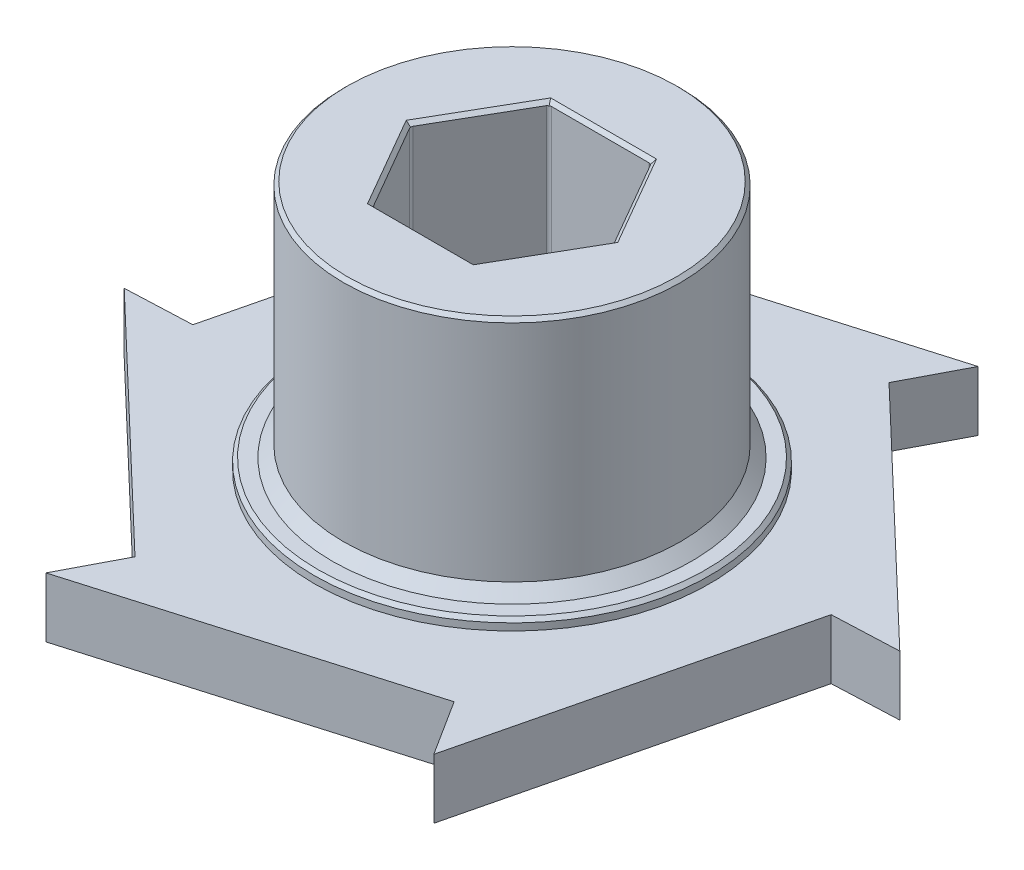
SolidWorks part; units mm, degrees
ref_plane "Front Plane" through (0, 0, 0) normal (0, 0, 1) x (1, 0, 0)
ref_plane "Top Plane" through (0, 0, 0) normal (0, 1, 0) x (1, 0, 0)
ref_plane "Right Plane" through (0, 0, 0) normal (1, 0, 0) x (0, 0, -1)
sketch "Sketch1" plane through (0, 0, 0) normal (0, 0, 1) x (1, 0, 0)
  line L0 (27.7876, 7.366) -> (0, 7.366)
  line L1 (0, 7.366) -> (0, 3.048)
  line L2 (0, 3.048) -> (27.7876, 3.048)
  line L3 (27.7876, 3.048) -> (27.7876, 7.366)
  line L4 (0, 7.366) -> (0, 3.048) construction
revolve "Revolve1" add sketch "Sketch1" angle 360 about L4
sketch "Sketch2" plane through (0, 7.366, 0) normal (0, 1, 0) x (-1, 0, 0)
  line L0 (27.7422, 1.5875) -> (25.86, 1.5875)
  line L1 (25.86, -1.5875) -> (27.7422, -1.5875)
  arc A0 (25.86, 1.5875) -> (25.86, -1.5875) centre (23.8125, 0) cw
  arc A1 (27.7422, -1.5875) -> (27.7422, 1.5875) centre (0, 0) ccw
extrude "Cut-Extrude1" cut sketch "Sketch2" against normal through all
sketch "Sketch3" plane through (0, 7.366, 0) normal (0, 1, 0) x (-1, 0, 0)
  arc A0 (27.522, -3.8329) -> (24.9505, -5.2112) centre (23.8125, 0) cw
  arc A1 (24.9505, -5.2112) -> (16.9883, -19.0022) centre (0, 0) cw
  arc A2 (16.9883, -19.0022) -> (17.0804, -21.9183) centre (11.9062, -20.6222) cw
  arc A3 (17.0804, -21.9183) -> (27.522, -3.8329) centre (0, 0) ccw
extrude "Cut-Extrude2" cut sketch "Sketch3" against normal through all
sketch "Sketch4" plane through (0, 7.366, 0) normal (0, 1, 0) x (-1, 0, 0)
  line L0 (15.2459, -23.2317) -> (14.3048, -21.6016)
  line L1 (11.5552, -23.1891) -> (12.4963, -24.8192)
  arc A0 (14.3048, -21.6016) -> (11.5552, -23.1891) centre (11.9063, -20.6222) cw
  arc A1 (12.4963, -24.8192) -> (15.2459, -23.2317) centre (0, 0) ccw
extrude "Cut-Extrude3" cut sketch "Sketch4" against normal through all
sketch "Sketch5" plane through (0, 7.366, 0) normal (0, 1, 0) x (-1, 0, 0)
  arc A0 (10.4416, -25.7512) -> (7.9622, -24.2134) centre (11.9063, -20.6222) cw
  arc A1 (7.9622, -24.2134) -> (-7.9622, -24.2134) centre (0, 0) cw
  arc A2 (-7.9622, -24.2134) -> (-10.4416, -25.7512) centre (-11.9063, -20.6222) cw
  arc A3 (-10.4416, -25.7512) -> (10.4416, -25.7512) centre (0, 0) ccw
extrude "Cut-Extrude4" cut sketch "Sketch5" against normal through all
sketch "Sketch6" plane through (0, 7.366, 0) normal (0, 1, 0) x (-1, 0, 0)
  line L0 (-12.4963, -24.8192) -> (-11.5552, -23.1891)
  line L1 (-14.3048, -21.6016) -> (-15.2459, -23.2317)
  arc A0 (-11.5552, -23.1891) -> (-14.3048, -21.6016) centre (-11.9062, -20.6222) cw
  arc A1 (-15.2459, -23.2317) -> (-12.4963, -24.8192) centre (0, 0) ccw
extrude "Cut-Extrude5" cut sketch "Sketch6" against normal through all
sketch "Sketch7" plane through (0, 7.366, 0) normal (0, 1, 0) x (-1, 0, 0)
  arc A0 (-17.0804, -21.9183) -> (-16.9883, -19.0022) centre (-11.9062, -20.6222) cw
  arc A1 (-16.9883, -19.0022) -> (-24.9505, -5.2112) centre (0, 0) cw
  arc A2 (-24.9505, -5.2112) -> (-27.522, -3.8329) centre (-23.8125, 0) cw
  arc A3 (-27.522, -3.8329) -> (-17.0804, -21.9183) centre (0, 0) ccw
extrude "Cut-Extrude6" cut sketch "Sketch7" against normal through all
sketch "Sketch8" plane through (0, 7.366, 0) normal (0, 1, 0) x (-1, 0, 0)
  line L0 (-27.7422, -1.5875) -> (-25.86, -1.5875)
  line L1 (-25.86, 1.5875) -> (-27.7422, 1.5875)
  arc A0 (-25.86, -1.5875) -> (-25.86, 1.5875) centre (-23.8125, 0) cw
  arc A1 (-27.7422, 1.5875) -> (-27.7422, -1.5875) centre (0, 0) ccw
extrude "Cut-Extrude7" cut sketch "Sketch8" against normal through all
sketch "Sketch9" plane through (0, 7.366, 0) normal (0, 1, 0) x (-1, 0, 0)
  arc A0 (-27.522, 3.8329) -> (-24.9505, 5.2112) centre (-23.8125, 0) cw
  arc A1 (-24.9505, 5.2112) -> (-16.9883, 19.0022) centre (0, 0) cw
  arc A2 (-16.9883, 19.0022) -> (-17.0804, 21.9183) centre (-11.9062, 20.6222) cw
  arc A3 (-17.0804, 21.9183) -> (-27.522, 3.8329) centre (0, 0) ccw
extrude "Cut-Extrude8" cut sketch "Sketch9" against normal through all
sketch "Sketch10" plane through (0, 7.366, 0) normal (0, 1, 0) x (-1, 0, 0)
  line L0 (-15.2459, 23.2317) -> (-14.3048, 21.6016)
  line L1 (-11.5552, 23.1891) -> (-12.4963, 24.8192)
  arc A0 (-14.3048, 21.6016) -> (-11.5552, 23.1891) centre (-11.9063, 20.6222) cw
  arc A1 (-12.4963, 24.8192) -> (-15.2459, 23.2317) centre (0, 0) ccw
extrude "Cut-Extrude9" cut sketch "Sketch10" against normal through all
sketch "Sketch11" plane through (0, 7.366, 0) normal (0, 1, 0) x (-1, 0, 0)
  arc A0 (-10.4416, 25.7512) -> (-7.9622, 24.2134) centre (-11.9062, 20.6222) cw
  arc A1 (-7.9622, 24.2134) -> (7.9622, 24.2134) centre (0, 0) cw
  arc A2 (7.9622, 24.2134) -> (10.4416, 25.7512) centre (11.9063, 20.6222) cw
  arc A3 (10.4416, 25.7512) -> (-10.4416, 25.7512) centre (0, 0) ccw
extrude "Cut-Extrude10" cut sketch "Sketch11" against normal through all
sketch "Sketch12" plane through (0, 7.366, 0) normal (0, 1, 0) x (-1, 0, 0)
  line L0 (12.4963, 24.8192) -> (11.5552, 23.1891)
  line L1 (14.3048, 21.6016) -> (15.2459, 23.2317)
  arc A0 (11.5552, 23.1891) -> (14.3048, 21.6016) centre (11.9062, 20.6222) cw
  arc A1 (15.2459, 23.2317) -> (12.4963, 24.8192) centre (0, 0) ccw
extrude "Cut-Extrude11" cut sketch "Sketch12" against normal through all
sketch "Sketch13" plane through (0, 7.366, 0) normal (0, 1, 0) x (-1, 0, 0)
  arc A0 (17.0804, 21.9183) -> (16.9883, 19.0022) centre (11.9062, 20.6222) cw
  arc A1 (16.9883, 19.0022) -> (24.9505, 5.2112) centre (0, 0) cw
  arc A2 (24.9505, 5.2112) -> (27.522, 3.8329) centre (23.8125, 0) cw
  arc A3 (27.522, 3.8329) -> (17.0804, 21.9183) centre (0, 0) ccw
extrude "Cut-Extrude12" cut sketch "Sketch13" against normal through all
sketch "Sketch14" plane through (0, 3.048, 0) normal (0, -1, 0) x (1, 0, 0)
  circle A0 centre (0, 0) radius 14.2748
extrude "Boss-Extrude1" add sketch "Sketch14" along normal blind 1.524
sketch "Sketch15" plane through (0, 1.524, 0) normal (0, -1, 0) x (1, 0, 0)
  circle A0 centre (0, 0) radius 9.2382
extrude "Boss-Extrude2" add sketch "Sketch15" along normal blind 1.524
sketch "Sketch16" plane through (0, 7.366, 0) normal (0, 1, 0) x (-1, 0, 0)
  circle A0 centre (0, 0) radius 14.2748
extrude "Boss-Extrude3" add sketch "Sketch16" along normal blind 0.762
sketch "Sketch17" plane through (0, 8.128, 0) normal (0, 1, 0) x (-1, 0, 0)
  circle A0 centre (0, 0) radius 12.1666
extrude "Boss-Extrude4" add sketch "Sketch17" along normal blind 17.272
sketch "Sketch18" plane through (0, 25.4, 0) normal (0, 1, 0) x (-1, 0, 0)
  line L0 (-3.6735, -6.3627) -> (3.6735, -6.3627)
  line L1 (3.6735, -6.3627) -> (7.347, 0)
  line L2 (7.347, 0) -> (3.6735, 6.3627)
  line L3 (3.6735, 6.3627) -> (-3.6735, 6.3627)
  line L4 (-3.6735, 6.3627) -> (-7.347, 0)
  line L5 (-7.347, 0) -> (-3.6735, -6.3627)
extrude "Cut-Extrude13" cut sketch "Sketch18" against normal through all
ref_plane "Plane1" through (0, 0, 0) normal (0, 0, -1) x (-1, 0, 0)
sketch "Sketch19" plane through (0, 0, 0) normal (0, 0, -1) x (-1, 0, 0)
  line L0 (21.2217, 3.048) -> (23.8125, 3.048)
  line L1 (23.8125, 3.048) -> (23.8125, 7.366)
  line L2 (23.8125, 7.366) -> (21.2217, 7.366)
  line L3 (21.2217, 7.366) -> (21.2217, 3.048)
  line L4 (23.8125, 3.048) -> (23.8125, 7.366) construction
revolve "Cut-Revolve1" cut sketch "Sketch19" angle 360 about L4
ref_plane "Plane2" through (0, 0, -20.6222) normal (0, 0, -1) x (-1, 0, 0)
sketch "Sketch20" plane through (0, 0, -20.6222) normal (0, 0, -1) x (-1, 0, 0)
  line L0 (9.3155, 3.048) -> (11.9063, 3.048)
  line L1 (11.9063, 3.048) -> (11.9063, 7.366)
  line L2 (11.9063, 7.366) -> (9.3155, 7.366)
  line L3 (9.3155, 7.366) -> (9.3155, 3.048)
  line L4 (11.9063, 3.048) -> (11.9063, 7.366) construction
revolve "Cut-Revolve2" cut sketch "Sketch20" angle 360 about L4
sketch "Sketch21" plane through (0, 0, -20.6222) normal (0, 0, -1) x (-1, 0, 0)
  line L0 (-14.497, 3.048) -> (-11.9062, 3.048)
  line L1 (-11.9062, 3.048) -> (-11.9062, 7.366)
  line L2 (-11.9062, 7.366) -> (-14.497, 7.366)
  line L3 (-14.497, 7.366) -> (-14.497, 3.048)
  line L4 (-11.9062, 3.048) -> (-11.9062, 7.366) construction
revolve "Cut-Revolve3" cut sketch "Sketch21" angle 360 about L4
sketch "Sketch22" plane through (0, 0, 0) normal (0, 0, -1) x (-1, 0, 0)
  line L0 (-26.4033, 3.048) -> (-23.8125, 3.048)
  line L1 (-23.8125, 3.048) -> (-23.8125, 7.366)
  line L2 (-23.8125, 7.366) -> (-26.4033, 7.366)
  line L3 (-26.4033, 7.366) -> (-26.4033, 3.048)
  line L4 (-23.8125, 3.048) -> (-23.8125, 7.366) construction
revolve "Cut-Revolve4" cut sketch "Sketch22" angle 360 about L4
ref_plane "Plane3" through (0, 0, 20.6222) normal (0, 0, -1) x (-1, 0, 0)
sketch "Sketch23" plane through (0, 0, 20.6222) normal (0, 0, -1) x (-1, 0, 0)
  line L0 (-14.4971, 3.048) -> (-11.9063, 3.048)
  line L1 (-11.9063, 3.048) -> (-11.9063, 7.366)
  line L2 (-11.9063, 7.366) -> (-14.4971, 7.366)
  line L3 (-14.4971, 7.366) -> (-14.4971, 3.048)
  line L4 (-11.9063, 3.048) -> (-11.9063, 7.366) construction
revolve "Cut-Revolve5" cut sketch "Sketch23" angle 360 about L4
sketch "Sketch24" plane through (0, 0, 20.6222) normal (0, 0, -1) x (-1, 0, 0)
  line L0 (9.3154, 3.048) -> (11.9062, 3.048)
  line L1 (11.9062, 3.048) -> (11.9062, 7.366)
  line L2 (11.9062, 7.366) -> (9.3154, 7.366)
  line L3 (9.3154, 7.366) -> (9.3154, 3.048)
  line L4 (11.9062, 3.048) -> (11.9062, 7.366) construction
revolve "Cut-Revolve6" cut sketch "Sketch24" angle 360 about L4
chamfer "Chamfer1" distance 0.254 angle 45 16 edges at (0, 8.128, 14.2748) (5.5103, 25.4, -3.1814) (0, 25.4, -6.3627) (-5.5103, 25.4, -3.1813) (-5.5103, 25.4, 3.1814) (0, 25.4, 6.3627) (5.5103, 25.4, 3.1813) (0, 1.524, -14.2748) (0, 0, -9.2382) (-5.5103, 0, 3.1814) (0, 0, 6.3627) (5.5103, 0, 3.1813) (5.5103, 0, -3.1814) (0, 0, -6.3627) (-5.5103, 0, -3.1813) (0, 25.4, 12.1666)
chamfer "Chamfer2" distance 0.8128 angle 45 1 edges at (0, 8.128, 12.1666)
fillet "Fillet1" radius 0.254 6 edges at (7.347, 12.7, 0) (-3.6735, 12.7, 6.3627) (3.6735, 12.7, 6.3627) (-3.6735, 12.7, -6.3627) (3.6735, 12.7, -6.3627) (-7.347, 12.7, 0)
fillet "Fillet2" radius 0.7874 24 edges at (-27.7422, 5.207, -1.5875) (-14.3048, 5.207, 21.6016) (12.4963, 5.207, 24.8192) (-11.5552, 5.207, 23.1891) (11.5552, 5.207, -23.1891) (12.4963, 5.207, -24.8192) (-14.3048, 5.207, -21.6016) (-15.2459, 5.207, 23.2317) (-25.86, 5.207, 1.5875) (11.5552, 5.207, 23.1891) (14.3048, 5.207, -21.6016) (14.3048, 5.207, 21.6016) (27.7422, 5.207, -1.5875) (-12.4963, 5.207, 24.8192) (-11.5552, 5.207, -23.1891) (-12.4963, 5.207, -24.8192) (-27.7422, 5.207, 1.5875) (25.86, 5.207, 1.5875) (-25.86, 5.207, -1.5875) (25.86, 5.207, -1.5875) (15.2459, 5.207, 23.2317) (-15.2459, 5.207, -23.2317) (27.7422, 5.207, 1.5875) (15.2459, 5.207, -23.2317)
fillet "Fillet3" radius 1.27 24 edges at (16.9883, 5.207, 19.0022) (-24.9505, 5.207, 5.2112) (7.9622, 5.207, -24.2134) (-10.4416, 5.207, 25.7512) (-7.9622, 5.207, 24.2134) (10.4416, 5.207, 25.7512) (24.9505, 5.207, -5.2112) (17.0804, 5.207, 21.9183) (-16.9883, 5.207, -19.0022) (27.522, 5.207, 3.8329) (-16.9883, 5.207, 19.0022) (27.522, 5.207, -3.8329) (7.9622, 5.207, 24.2134) (17.0804, 5.207, -21.9183) (24.9505, 5.207, 5.2112) (10.4416, 5.207, -25.7512) (16.9883, 5.207, -19.0022) (-10.4416, 5.207, -25.7512) (-7.9622, 5.207, -24.2134) (-17.0804, 5.207, -21.9183) (-24.9505, 5.207, -5.2112) (-27.522, 5.207, -3.8329) (-27.522, 5.207, 3.8329) (-17.0804, 5.207, 21.9183)
sketch "Sketch25" plane through (0, 7.366, 0) normal (0, 1, 0) x (1, 0, 0)
  circle A0 centre (0, 0) radius 25.4889
  circle A1 centre (0, 0) radius 28.0506
extrude "Cut-Extrude14" cut sketch "Sketch25" against normal through all
sketch "Sketch26" plane through (0, 7.366, 0) normal (0, 1, 0) x (1, 0, 0)
  line L0 (-1.3402, -0.851) -> (-14.9768, 20.6247)
  line L1 (-1.407, 0.7351) -> (10.3731, 23.2827)
  line L2 (-0.0669, 1.5861) -> (25.3499, 2.6579)
  line L3 (1.3402, 0.851) -> (14.9768, -20.6247)
  line L4 (1.407, -0.7351) -> (-10.3731, -23.2827)
  line L5 (0.0669, -1.5861) -> (-25.3499, -2.6579)
  line L6 (-20.5917, -2.4573) -> (-14.9768, 20.6247)
  line L7 (-12.4239, 16.6043) -> (10.3731, 23.2827)
  line L9 (8.1678, 19.0615) -> (25.3499, 2.6579)
  line L10 (14.9768, -20.6247) -> (20.5917, 2.4573)
  line L11 (12.4239, -16.6043) -> (-10.3731, -23.2827)
  line L12 (-25.3499, -2.6579) -> (-8.1678, -19.0615)
  circle A0 centre (0, 0) radius 1.5875 construction
  arc A1 (10.935, 23.0241) -> (-10.935, 23.0241) centre (0, 0) ccw construction
  arc A2 (10.935, 23.0241) -> (14.4719, 20.9821) centre (11.9062, 20.6222) ccw construction
  arc A3 (25.407, 2.042) -> (14.4719, 20.9821) centre (0, 0) ccw construction
  arc A4 (25.407, 2.042) -> (25.407, -2.042) centre (23.8125, 0) ccw construction
  arc A5 (14.4719, -20.9821) -> (25.407, -2.042) centre (0, 0) ccw construction
  arc A6 (14.4719, -20.9821) -> (10.935, -23.0241) centre (11.9063, -20.6222) ccw construction
  arc A7 (-10.935, -23.0241) -> (10.935, -23.0241) centre (0, 0) ccw construction
  arc A8 (-10.935, -23.0241) -> (-14.4719, -20.9821) centre (-11.9062, -20.6222) ccw construction
  arc A9 (-25.407, -2.042) -> (-14.4719, -20.9821) centre (0, 0) ccw construction
  arc A10 (-25.407, -2.042) -> (-25.407, 2.042) centre (-23.8125, 0) ccw construction
  circle A11 centre (0, 0) radius 25.4889
  arc A19 (-14.4719, 20.9821) -> (-25.407, 2.042) centre (0, 0) ccw construction
  arc A36 (-14.4719, 20.9821) -> (-10.935, 23.0241) centre (-11.9063, 20.6222) ccw construction
  point P32 (0, 0)
  arc M27 (-10.935, -23.0241) -> (10.935, -23.0241) centre (0, 0) ccw
  arc M28 (10.935, -23.0241) -> (14.4719, -20.9821) centre (11.9063, -20.6222) cw
  arc M29 (14.4719, -20.9821) -> (25.407, -2.042) centre (0, 0) ccw
  arc M30 (25.407, -2.042) -> (25.407, 2.042) centre (23.8125, 0) cw
  arc M31 (25.407, 2.042) -> (14.4719, 20.9821) centre (0, 0) ccw
  arc M32 (14.4719, 20.9821) -> (10.935, 23.0241) centre (11.9062, 20.6222) cw
  arc M33 (10.935, 23.0241) -> (-10.935, 23.0241) centre (0, 0) ccw
  arc M34 (-10.935, 23.0241) -> (-14.4719, 20.9821) centre (-11.9063, 20.6222) cw
  arc M35 (-14.4719, 20.9821) -> (-25.407, 2.042) centre (0, 0) ccw
  arc M36 (-25.407, 2.042) -> (-25.407, -2.042) centre (-23.8125, 0) cw
  arc M37 (-25.407, -2.042) -> (-14.4719, -20.9821) centre (0, 0) ccw
  arc M38 (-14.4719, -20.9821) -> (-10.935, -23.0241) centre (-11.9062, -20.6222) cw
  dimension "D1" = 3.175
  dimension "D2" = 4.7625
  dimension "D8" = 50.9778
  dimension "D3" = 4.7625
  dimension "D4" = 4.7625
  dimension "D5" = 4.7625
  dimension "D6" = 4.7625
  dimension "D7" = 4.7625
extrude "Cut-Extrude15" cut sketch "Sketch26" against normal through all contours L0 L7 M33 M34 | L5 L6 M35 M36 | L12 L4 M37 M38 | L3 L11 M27 M28 | L10 L2 M29 M30 | L1 L9 M31 M32 | L0 M34 M35 | L1 M32 M33 | L2 M30 M31 | L3 M28 M29 | L4 M38 M27 | L5 M36 M37 | A11
